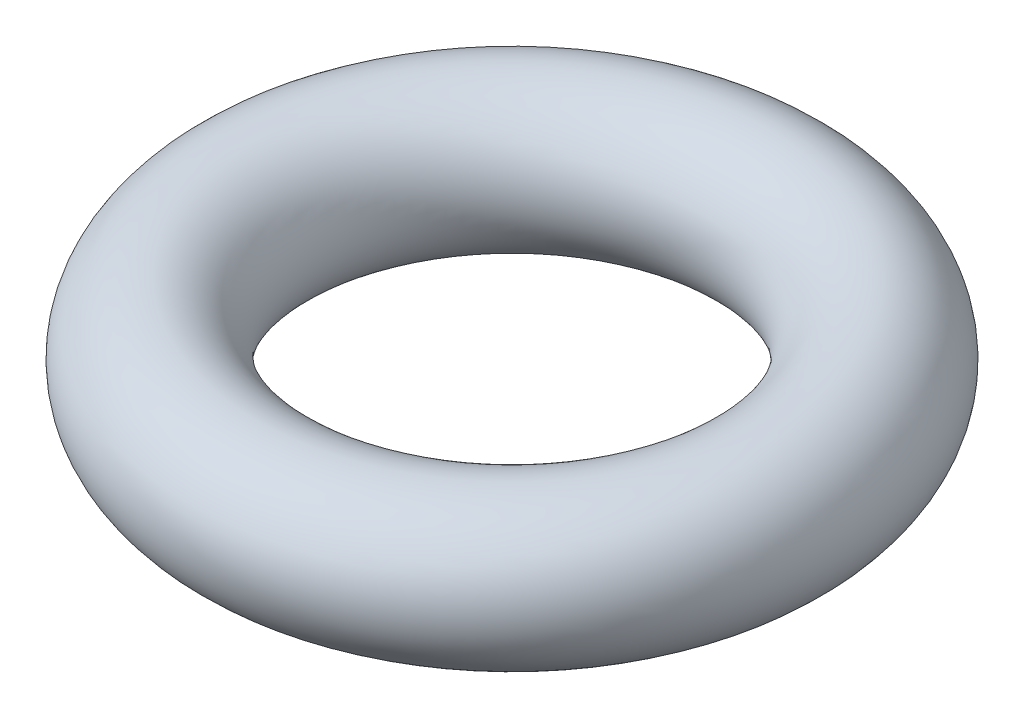
SolidWorks part; units mm, degrees
ref_plane "Front" through (0, 0, 0) normal (0, 0, 1) x (1, 0, 0)
ref_plane "Top" through (0, 0, 0) normal (0, 1, 0) x (1, 0, 0)
ref_plane "Right" through (0, 0, 0) normal (1, 0, 0) x (0, 0, -1)
sketch "Sketch1" plane through (0, 0, 0) normal (0, 0, 1) x (1, 0, 0)
  line L0 (0, 0) -> (0, 1.574) construction
  line L1 (2.5, -1.574) -> (2.5, 1.574) construction
  line L2 (4.5, -1.574) -> (4.5, 1.574) construction
  line L3 (4.5, 0) -> (2.5, 0) construction
  circle A0 centre (3.5, 0) radius 1
  dimension "D1" = 2.5
  dimension "D2" = 4.5
revolve "Revolve1" add sketch "Sketch1" angle 360 about L0
